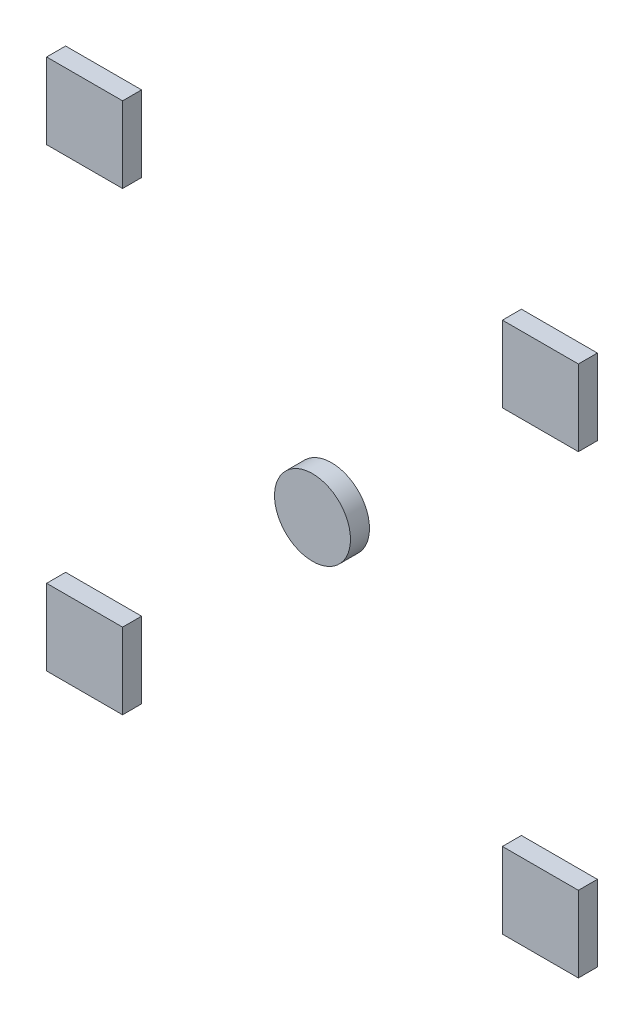
SolidWorks part; units mm, degrees
ref_plane "Alzado" through (0, 0, 0) normal (0, 0, 1) x (1, 0, 0)
ref_plane "Planta" through (0, 0, 0) normal (0, 1, 0) x (1, 0, 0)
ref_plane "Vista lateral" through (0, 0, 0) normal (1, 0, 0) x (0, 0, -1)
sketch "Croquis2" plane through (0, 0, 0) normal (0, 0, 1) x (1, 0, 0)
  line L0 (140, 0) -> (140, 20)
  line L1 (0, 0) -> (20, 0)
  line L2 (0, 0) -> (0, 20)
  line L3 (0, 20) -> (20, 20)
  line L4 (20, 0) -> (20, 20)
  line L5 (120, 20) -> (140, 20)
  line L6 (120, 0) -> (120, 20)
  line L7 (120, 0) -> (140, 0)
  line L8 (20, 120) -> (20, 140)
  line L9 (0, 140) -> (20, 140)
  line L10 (0, 120) -> (0, 140)
  line L11 (0, 120) -> (20, 120)
  line L12 (140, 120) -> (140, 140)
  line L13 (120, 140) -> (140, 140)
  line L14 (120, 120) -> (120, 140)
  line L15 (120, 120) -> (140, 120)
  line L16 (20, 20) -> (120, 120) construction
  line L17 (120, 120) -> (119.4424, 119.4369) construction
  circle A0 centre (70, 70) radius 10
  dimension "D3" = 20
  dimension "D1" = 20
  dimension "D2" = 20
extrude "Extruir1" add sketch "Croquis2" along normal blind 5
